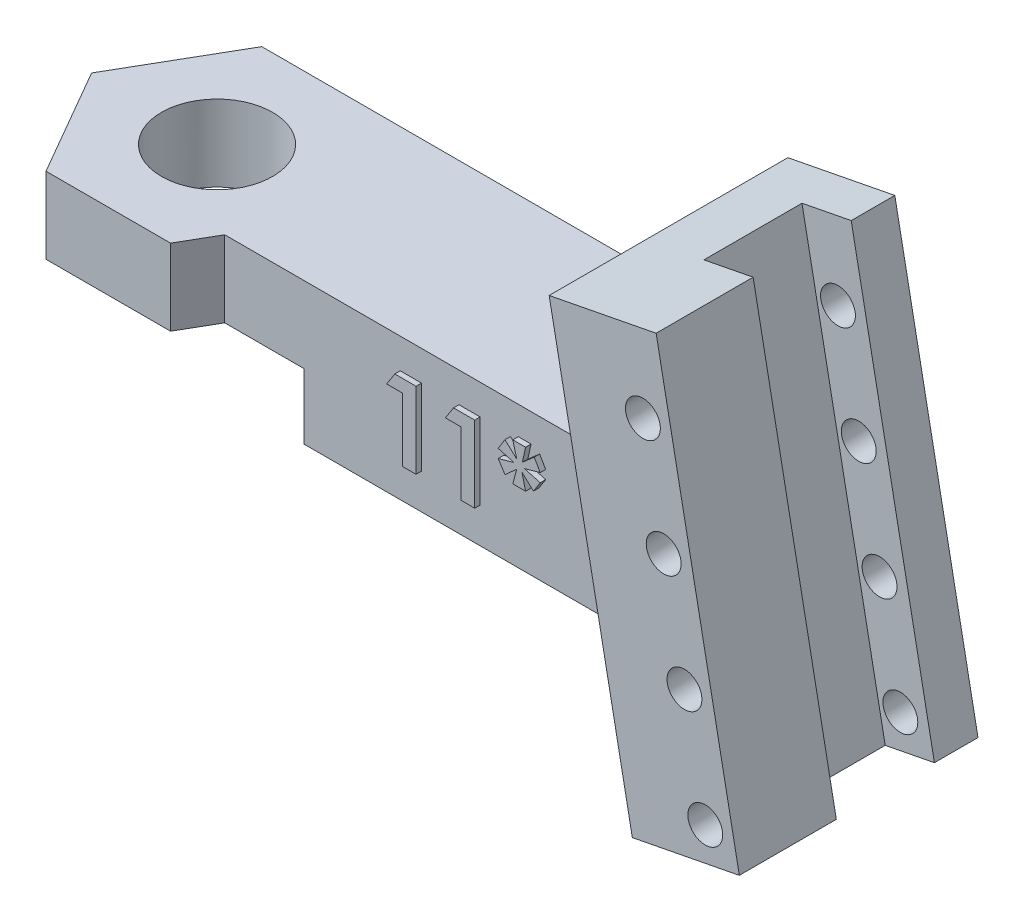
SolidWorks part; units mm, degrees
ref_plane "Front Plane" through (0, 0, 0) normal (0, 0, 1) x (1, 0, 0)
ref_plane "Top Plane" through (0, 0, 0) normal (0, 1, 0) x (1, 0, 0)
ref_plane "Right Plane" through (0, 0, 0) normal (1, 0, 0) x (0, 0, -1)
sketch "Sketch1" plane through (0, 0, 0) normal (0, 1, 0) x (1, 0, 0)
  line L1 (0, 0) -> (25, 0)
  line L2 (0, 0) -> (0, -6.75)
  line L3 (0, -6.75) -> (25, -6.75)
  line L4 (25, 0) -> (25, -6.75)
  dimension "D1" = 6.75
  dimension "D2" = 25
extrude "Boss-Extrude1" add sketch "Sketch1" along normal blind 6.5
ref_plane "Plane1" through (0, 0, 3.375) normal (0, 0, 1) x (1, 0, 0)
sketch "Sketch5" plane through (0, 6.5, 0) normal (0, 1, 0) x (1, 0, 0)
  line L0 (0, 0) -> (0, -6.75) construction
  line L1 (-5.7158, -3.375) -> (-2.8579, -8.325)
  line L2 (-2.8579, -8.325) -> (2.8579, -8.325)
  line L3 (2.8579, -8.325) -> (5.7158, -3.375)
  line L4 (5.7158, -3.375) -> (2.8579, 1.575)
  line L5 (2.8579, 1.575) -> (-2.8579, 1.575)
  line L6 (-2.8579, 1.575) -> (-5.7158, -3.375)
  circle A0 centre (0, -3.375) radius 4.95 construction
  dimension "D1" = 4.95
extrude "Boss-Extrude4" add sketch "Sketch5" against normal up to surface (6.5 mm away) up to face at (12.5, 0, 3.375)
sketch "Sketch3" plane through (0, 0, 3.375) normal (0, 0, 1) x (1, 0, 0)
  line L0 (21.2757, 14.1555) -> (26.1838, 15.1096)
  line L1 (26.1838, 15.1096) -> (30, -4.523)
  line L2 (30, -4.523) -> (25.0919, -5.477)
  line L3 (25.0919, -5.477) -> (21.2757, 14.1555)
  line L4 (3.7672, 6.5) -> (25, 6.5) construction
  point P6 (27.5459, -5)
  dimension "D1" = 30
  dimension "D2" = 5
  dimension "D3" = 20
  dimension "D4" = 79
  dimension "D6" = 5
extrude "Boss-Extrude3" add sketch "Sketch3" against normal up to surface (4.95 mm away) and the other way blind 6 up to face at (0, 3.25, -1.575)
sketch "Sketch4" plane through (-1.8768, 9.6551, 0) normal (-0.1908, 0.9816, 0) x (0.9816, 0.1908, 0)
  line L0 (28.5858, -9.375) -> (28.5858, 1.575) construction
  line L1 (26.2858, -0.425) -> (28.5858, -0.425)
  line L2 (26.2858, -0.425) -> (26.2858, -4.925)
  line L3 (26.2858, -4.925) -> (28.5858, -4.925)
  line L4 (28.5858, -0.425) -> (28.5858, -4.925)
  line L6 (28.5858, 1.575) -> (23.5858, 1.575) construction
  dimension "D1" = 4.5
  dimension "D2" = 2.3
  dimension "D3" = 2
extrude "Cut-Extrude1" cut sketch "Sketch4" against normal blind 23 contours L2 L3 L4 L1
sketch "Sketch6" plane through (0, 6.5, 0) normal (0, 1, 0) x (1, 0, 0)
  circle A0 centre (0, -3.3356) radius 2.55
  dimension "D1" = 5.1
extrude "Cut-Extrude2" cut sketch "Sketch6" against normal blind 10
sketch "Sketch7" plane through (0, 0, -1.575) normal (0, 0, -1) x (-1, 0, 0)
  line L0 (-2.8579, 0) -> (-24.0272, 0)
  line L1 (-24.0272, 0) -> (-25.0919, -5.477)
  line L2 (-25.0919, -5.477) -> (-30, -4.523)
  line L3 (-30, -4.523) -> (-26.1838, 15.1096)
  line L4 (-26.1838, 15.1096) -> (-21.2757, 14.1555)
  line L5 (-21.2757, 14.1555) -> (-22.7638, 6.5)
  line L6 (-22.7638, 6.5) -> (-2.8579, 6.5)
  line L7 (-2.8579, 6.5) -> (-2.8579, 0)
  dimension "D1" = 20
extrude "Boss-Extrude5" add sketch "Sketch7" against normal up to surface (1.575 mm away) up to face at (13.5814, 3.25, 0)
sketch "Sketch8" plane through (0, 0, 0) normal (0, -1, 0) x (-1, 0, 0)
  line L1 (-4.6765, -11.475) -> (4.6765, -11.475)
  line L2 (4.6765, -11.475) -> (9.3531, -3.375)
  line L3 (9.3531, -3.375) -> (4.6765, 4.725)
  line L4 (4.6765, 4.725) -> (-4.6765, 4.725)
  line L5 (-4.6765, 4.725) -> (-9.3531, -3.375)
  line L6 (-9.3531, -3.375) -> (-4.6765, -11.475)
  circle A0 centre (0, -3.375) radius 8.1 construction
  dimension "D1" = 16.2
extrude "Cut-Extrude3" cut sketch "Sketch8" against normal blind 3
sketch "Sketch9" plane through (0, 0, -1.575) normal (0, 0, -1) x (-1, 0, 0)
  line L0 (-30, -4.523) -> (-26.1838, 15.1096) construction
  line L1 (-25.0919, -5.477) -> (-30, -4.523) construction
  line L2 (-28.4377, -3.2986) -> (-25.5755, 11.4258) construction
  line L3 (-30, -4.523) -> (-26.1838, 15.1096) construction
  circle A0 centre (-28.4377, -3.2986) radius 0.8
  circle A4 centre (-27.4836, 1.6095) radius 0.8
  circle A5 centre (-26.5296, 6.5177) radius 0.8
  circle A6 centre (-25.5755, 11.4258) radius 0.8
  dimension "D1" = 1.6
  dimension "D2" = 1.3
  dimension "D5" = 5
  dimension "D3" = 1.5
  dimension "D4" = 5
  dimension "D6" = 5
extrude "Cut-Extrude4" cut sketch "Sketch9" against normal up to surface (10.95 mm away) up to face at (25.6378, 4.8163, 9.375)
sketch "Sketch10" plane through (0, 0, 6.75) normal (0, 0, 1) x (1, 0, 0)
  text T0 "<b>11*</b>"
extrude "Boss-Extrude6" add sketch "Sketch10" along normal blind 0.25
